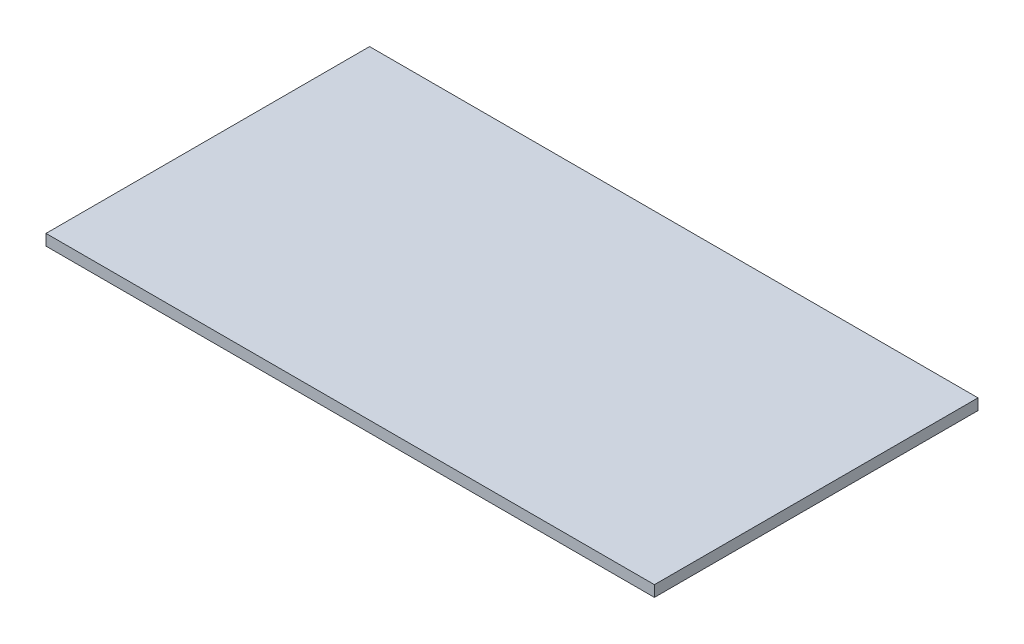
SolidWorks part; units mm, degrees
ref_plane "Front Plane" through (0, 0, 0) normal (0, 0, 1) x (1, 0, 0)
ref_plane "Top Plane" through (0, 0, 0) normal (0, 1, 0) x (1, 0, 0)
ref_plane "Right Plane" through (0, 0, 0) normal (1, 0, 0) x (0, 0, -1)
sketch "Sketch1" plane through (0, 0, 0) normal (0, 1, 0) x (1, 0, 0)
  line L1 (-110, -58.5) -> (110, -58.5)
  line L2 (-110, -58.5) -> (-110, 58.5)
  line L3 (-110, 58.5) -> (110, 58.5)
  line L4 (110, -58.5) -> (110, 58.5)
  line L5 (-110, -58.5) -> (110, 58.5) construction
  line L6 (-110, 58.5) -> (110, -58.5) construction
  point P0 (0, 0)
  dimension "D1" = 220
  dimension "D2" = 117
extrude "Boss-Extrude1" add sketch "Sketch1" along normal blind 4
